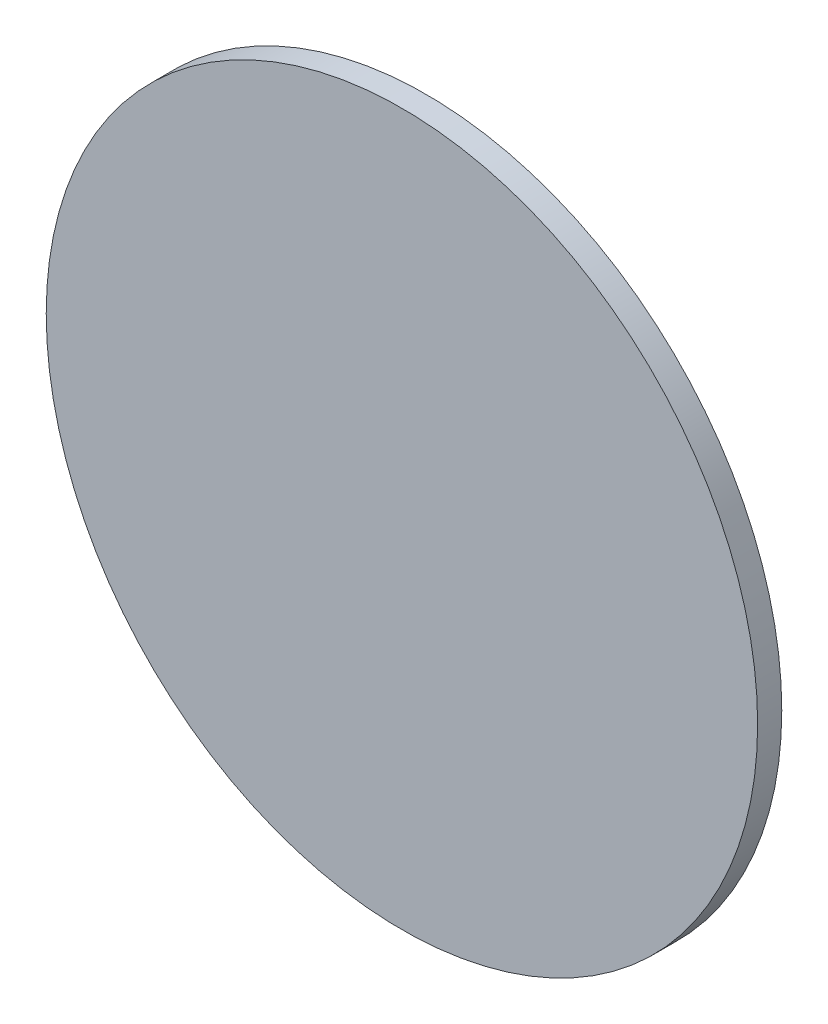
SolidWorks part; units mm, degrees
ref_plane "Front Plane" through (0, 0, 0) normal (0, 0, 1) x (1, 0, 0)
ref_plane "Top Plane" through (0, 0, 0) normal (0, 1, 0) x (1, 0, 0)
ref_plane "Right Plane" through (0, 0, 0) normal (1, 0, 0) x (0, 0, -1)
sketch "Sketch1" plane through (0, 0, 0) normal (0, 0, 1) x (1, 0, 0)
  circle A0 centre (0, 0) radius 147.418
extrude "Boss-Extrude1" add sketch "Sketch1" along normal blind 10
